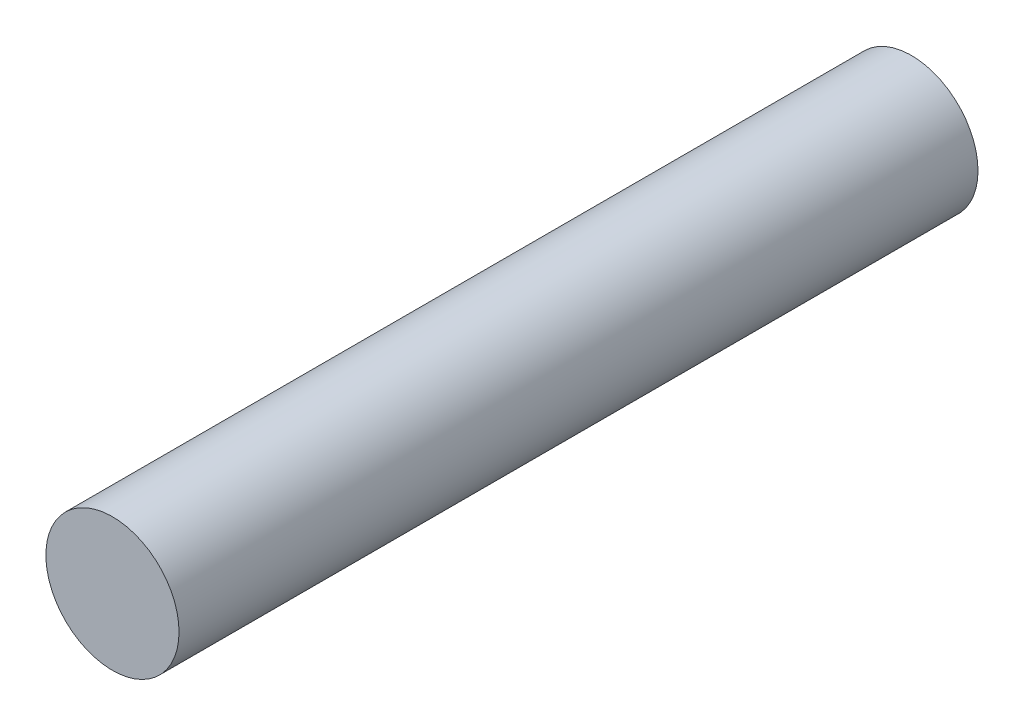
SolidWorks part; units mm, degrees
ref_plane "Front Plane" through (0, 0, 0) normal (0, 0, 1) x (1, 0, 0)
ref_plane "Top Plane" through (0, 0, 0) normal (0, 1, 0) x (1, 0, 0)
ref_plane "Right Plane" through (0, 0, 0) normal (1, 0, 0) x (0, 0, -1)
sketch "Sketch2" plane through (0, 0, 0) normal (0, 0, 1) x (1, 0, 0)
  circle A0 centre (0, 0) radius 4.7625
  dimension "D1" = 9.525
extrude "Boss-Extrude2" add sketch "Sketch2" along normal blind 57.15 contours A0
